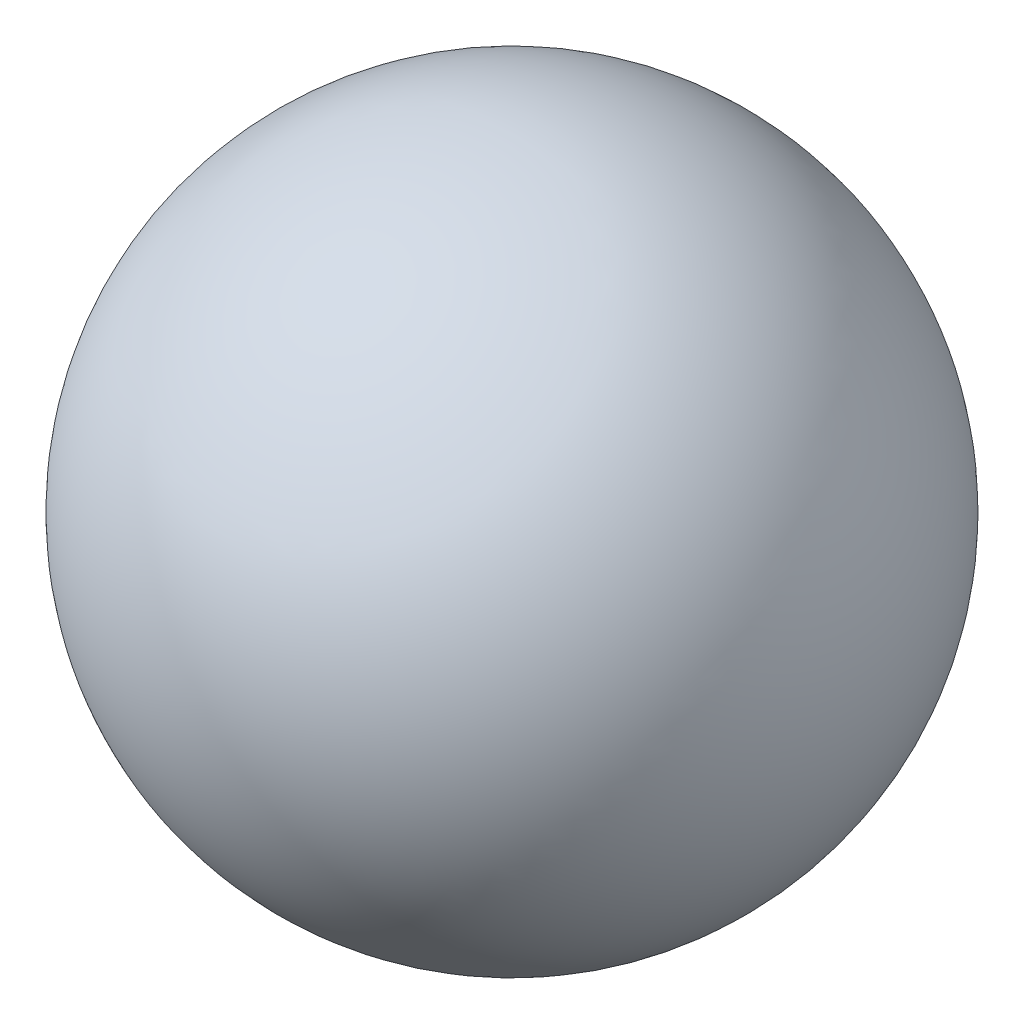
SolidWorks part; units mm, degrees
material "AISI 304"
ref_plane "Front" through (0, 0, 0) normal (0, 0, 1) x (1, 0, 0)
ref_plane "Top" through (0, 0, 0) normal (0, 1, 0) x (1, 0, 0)
ref_plane "Right" through (0, 0, 0) normal (1, 0, 0) x (0, 0, -1)
sketch "Sketch2" plane through (0, 0, 0) normal (0, 1, 0) x (1, 0, 0)
  line L0 (0, 0) -> (0, 8) construction
  line L1 (0, 7.5) -> (3.3833, 7.5) construction
  line L2 (1.9365, 7.5) -> (0, 7.5)
  line L3 (0, 7.5) -> (0, 0)
  line L4 (0, 4) -> (4, 4) construction
  arc A0 (0, 8) -> (0, 0) centre (0, 4) cw construction
  arc A1 (1.9365, 7.5) -> (0, 0) centre (0, 4) cw
  dimension "D1" = 8
  dimension "D2" = 0.5
revolve "Revolve1" add sketch "Sketch2" angle 360 about L3
hole_wizard "M3x0.5 Tapped Hole1" positions "Sketch3" profile "Sketch5" tap size "M3x0.5" standard "ANSI Metric"
sketch "Sketch3" plane through (0, 0, -7.5) normal (0, 0, -1) x (-1, 0, 0)
  point P3 (0, 0)
sketch "Sketch5" plane through (0, 0, -7.5) normal (1, 0, 0) x (0, 1, 0)
  line L0 (0, 0) -> (0, 6.7511)
  line L1 (0, 6.7511) -> (1.25, 6)
  line L2 (1.25, 6) -> (1.25, 0)
  line L5 (1.25, 0) -> (0, 0)
  line L10 (0, 6.7511) -> (-1.25, 6) construction
  line L11 (0, -6.35) -> (0, 107.95) construction
  dimension "Tap Drill Dia." = 2.5
  dimension "Tap Drill Depth" = 6
  dimension "Drill Angle" = 118
cosmetic thread "Hole Thread1" parameters "D1"=5, "D2"=3
